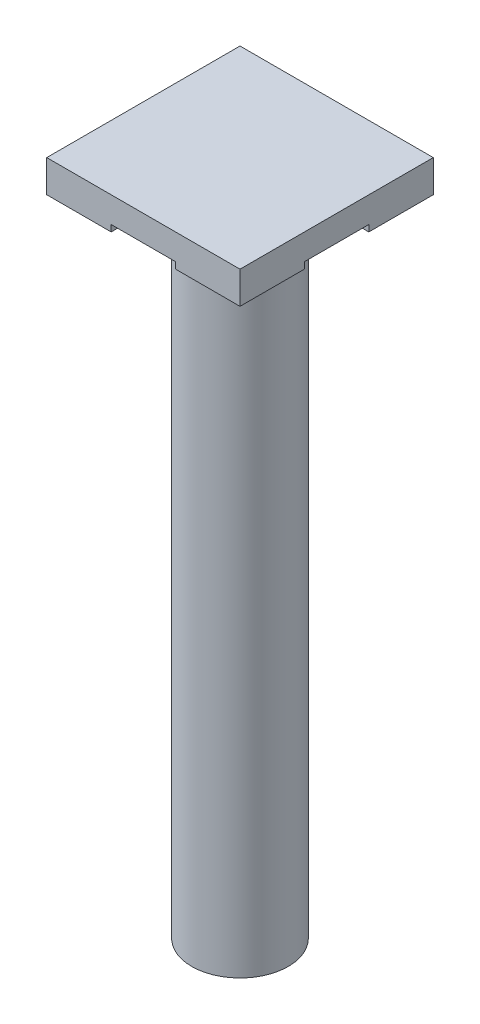
SolidWorks part; units mm, degrees
ref_plane "Front Plane" through (0, 0, 0) normal (0, 0, 1) x (1, 0, 0)
ref_plane "Top Plane" through (0, 0, 0) normal (0, 1, 0) x (1, 0, 0)
ref_plane "Right Plane" through (0, 0, 0) normal (1, 0, 0) x (0, 0, -1)
sketch "Sketch1" plane through (0, 0, 0) normal (0, 1, 0) x (1, 0, 0)
  circle A0 centre (0, 0) radius 19.05
  dimension "D1" = 38.1
extrude "Boss-Extrude1" add sketch "Sketch1" along normal blind 254
sketch "Sketch5" plane through (0, 254, 0) normal (0, 1, 0) x (1, 0, 0)
  line L1 (-38.1, 38.1) -> (38.1, 38.1)
  line L2 (-38.1, 38.1) -> (-38.1, -38.1)
  line L3 (-38.1, -38.1) -> (38.1, -38.1)
  line L4 (38.1, 38.1) -> (38.1, -38.1)
  dimension "D1" = 76.2
  dimension "D2" = 76.2
  dimension "D3" = 38.1
  dimension "D4" = 38.1
extrude "Boss-Extrude3" add sketch "Sketch5" along normal blind 12.7
sketch "Sketch6" plane through (0, 254, 0) normal (0, -1, 0) x (1, 0, 0)
  line L0 (-38.1, -38.1) -> (-38.1, 38.1) construction
  line L1 (-38.1, 12.7) -> (-29.21, 12.7)
  line L2 (-38.1, 12.7) -> (-38.1, -12.7)
  line L3 (-38.1, -12.7) -> (-29.21, -12.7)
  line L4 (-29.21, 12.7) -> (-29.21, -12.7)
  line L5 (-38.1, 38.1) -> (38.1, 38.1) construction
  line L6 (-12.7, 38.1) -> (12.7, 38.1)
  line L7 (-12.7, 38.1) -> (-12.7, 29.21)
  line L8 (-12.7, 29.21) -> (12.7, 29.21)
  line L9 (12.7, 38.1) -> (12.7, 29.21)
  line L10 (38.1, 38.1) -> (38.1, -38.1) construction
  line L11 (38.1, 12.7) -> (29.21, 12.7)
  line L12 (38.1, 12.7) -> (38.1, -12.7)
  line L13 (38.1, -12.7) -> (29.21, -12.7)
  line L14 (29.21, 12.7) -> (29.21, -12.7)
  line L15 (38.1, -38.1) -> (-38.1, -38.1) construction
  line L16 (-12.7, -38.1) -> (12.7, -38.1)
  line L17 (-12.7, -38.1) -> (-12.7, -29.21)
  line L18 (-12.7, -29.21) -> (12.7, -29.21)
  line L19 (12.7, -38.1) -> (12.7, -29.21)
  dimension "D1" = 25.4
  dimension "D2" = 25.4
  dimension "D3" = 25.4
  dimension "D4" = 25.4
  dimension "D5" = 25.4
  dimension "D6" = 25.4
  dimension "D7" = 25.4
  dimension "D8" = 25.4
  dimension "D9" = 8.89
  dimension "D10" = 8.89
  dimension "D11" = 8.89
  dimension "D12" = 8.89
extrude "Cut-Extrude1" cut sketch "Sketch6" against normal blind 2.54
